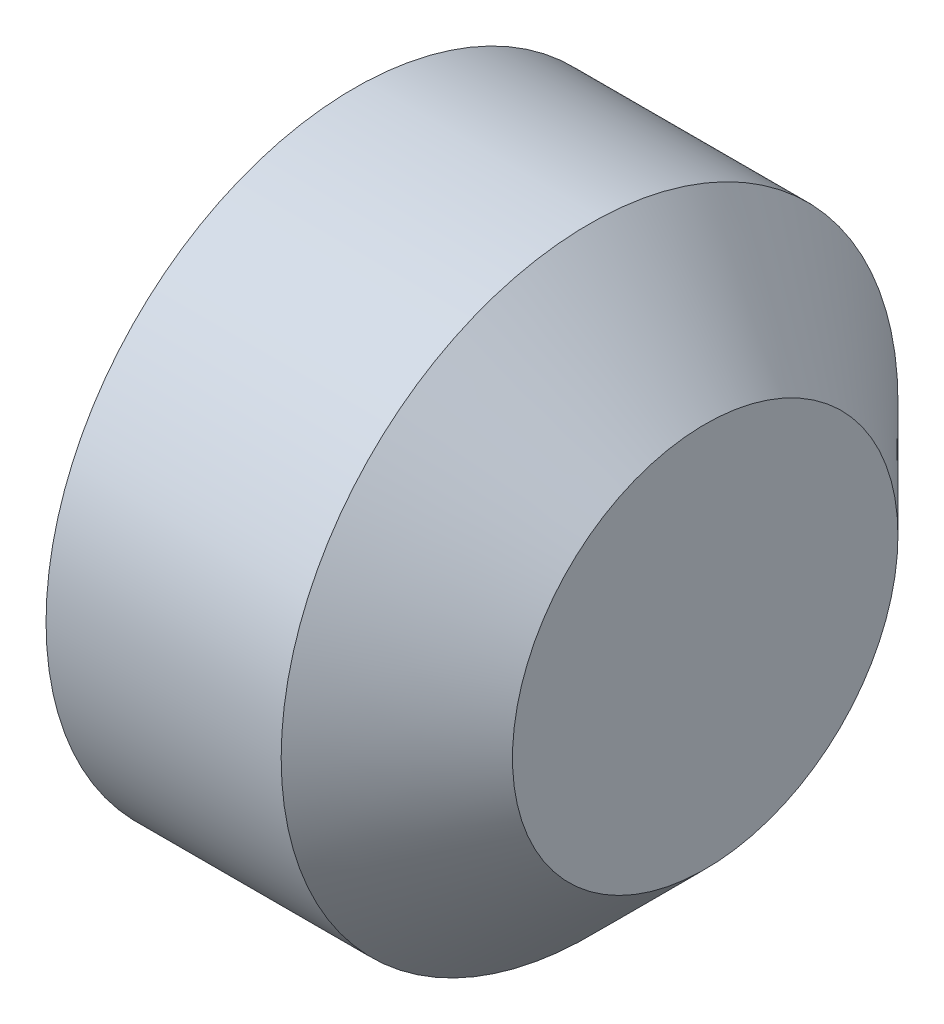
SolidWorks part; units mm, degrees
ref_plane "Спереди" through (0, 0, 0) normal (0, 0, 1) x (1, 0, 0)
ref_plane "Сверху" through (0, 0, 0) normal (0, 1, 0) x (1, 0, 0)
ref_plane "Справа" through (0, 0, 0) normal (1, 0, 0) x (0, 0, -1)
ref_plane "Плоскость1" through (0, 0, 0) normal (0, 0, -1) x (-1, 0, 0)
sketch "Эскиз1" plane through (0, 0, 0) normal (0, 0, -1) x (-1, 0, 0)
  line L0 (-2.5, 2) -> (-2.5, 0)
  line L1 (-2.5, 0) -> (0, 0)
  line L2 (0, 0) -> (0, 2)
  line L3 (0, 2) -> (-2.5, 2)
  line L4 (-2.5, 0) -> (0, 0) construction
revolve "Повернуть1" add sketch "Эскиз1" angle 360 about L4
sketch "Эскиз2" plane through (0, 0, 0) normal (-1, 0, 0) x (0, 0, 1)
  line L0 (1.1547, 0) -> (0.5774, 1)
  line L1 (0.5774, 1) -> (-0.5774, 1)
  line L2 (-0.5774, 1) -> (-1.1547, 0)
  line L3 (-1.1547, 0) -> (-0.5774, -1)
  line L4 (-0.5774, -1) -> (0.5774, -1)
  line L5 (0.5774, -1) -> (1.1547, 0)
extrude "Вырез-Вытянуть1" cut sketch "Эскиз2" against normal blind 1.5
chamfer "Фаска1" distance 0.75 angle 45 1 edges at (2.5, 0, 2)
chamfer "Фаска2" distance 0.39 angle 30 1 edges at (0, 0, 2)
